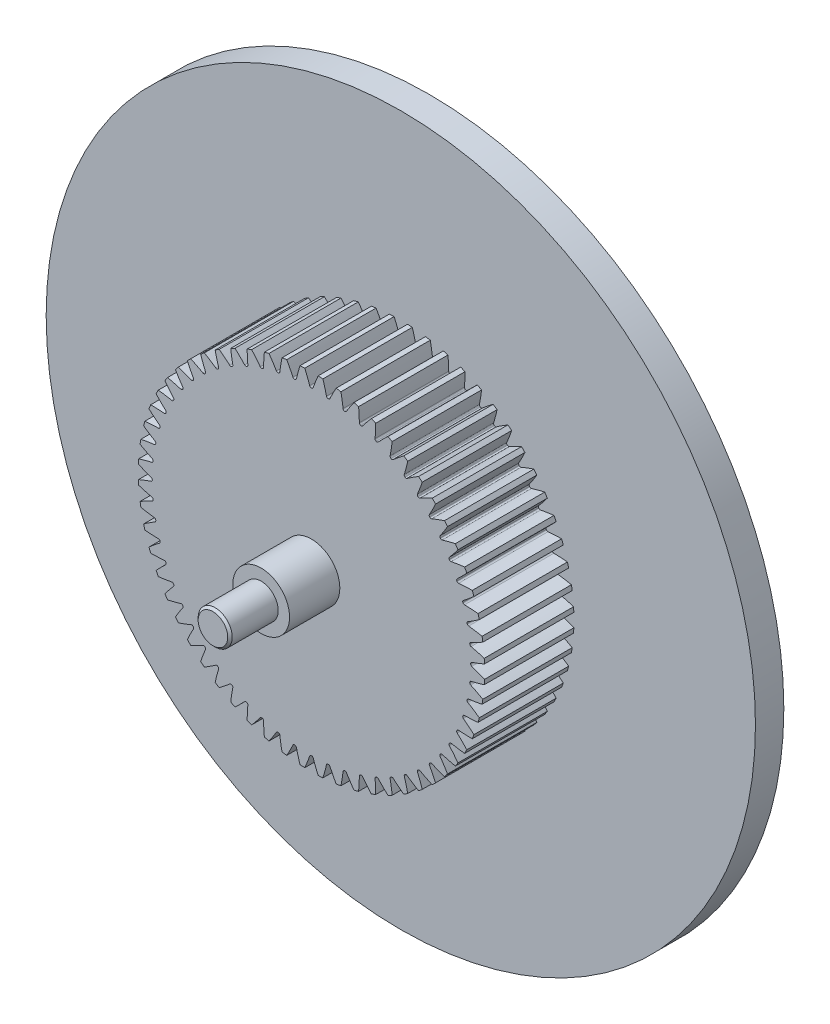
SolidWorks part; units mm, degrees
ref_plane "Front Plane" through (0, 0, 0) normal (0, 0, 1) x (1, 0, 0)
ref_plane "Top Plane" through (0, 0, 0) normal (0, 1, 0) x (1, 0, 0)
ref_plane "Right Plane" through (0, 0, 0) normal (1, 0, 0) x (0, 0, -1)
sketch "Sketch1" plane through (0, 0, 0) normal (0, 0, 1) x (1, 0, 0)
  line L0 (-762, 0) -> (762, 0) construction
  circle A0 centre (0, 0) radius 15.5 construction
  circle A1 centre (0, 0) radius 15 construction
  circle A2 centre (0, 0) radius 14.25 construction
  circle A3 centre (0, 0) radius 7 construction
  circle A4 centre (0, 0) radius 3 construction
  dimension "D2" = 0.5
  dimension "D3" = 1.25
  dimension "D1" = 1.25
sketch "Sketch2" plane through (0, 0, 0) normal (1, 0, 0) x (0, 0, -1)
  line L0 (0, 0) -> (-3, 0) construction
  line L1 (-3, 0) -> (-8, 0) construction
  dimension "Overall Width" = 8
  dimension "Face Width" = 3
sketch "Sketch4" plane through (0, 0, 0) normal (1, 0, 0) x (0, 0, -1)
  line L0 (-8, 3) -> (-8, 7)
  line L1 (-8, 7) -> (-3, 7) construction
  line L2 (-3, 7) -> (-3, 15.5) construction
  line L3 (-3, 15.5) -> (0, 15.5)
  line L4 (0, 15.5) -> (0, 3)
  line L5 (-3, 7) -> (-3, 0) construction
  line L6 (0, 15.5) -> (0, -15.5) construction
  line L7 (-3, 7) -> (0, 7) construction
  line L8 (-3, 15.5) -> (-8, 15.5)
  line L9 (-8, 15.5) -> (-8, 7)
  line L12 (-8, 3) -> (0, 3)
revolve "Revolve1" add sketch "Sketch4" angle 360 about L1
sketch "Sketch7" plane through (0, 0, 3) normal (0, 0, 1) x (1, 0, 0)
  line L0 (0, 0) -> (0, 15.5) construction
  line L1 (0.3927, 14.9949) -> (0.5873, 15.4889) construction
  line L3 (0.8112, 15.4788) -> (0.785, 14.9794) construction
  line L4 (0.785, 14.9794) -> (0.7458, 14.2305) construction
  line L5 (0, 0) -> (0.7458, 14.2305) construction
  line L6 (0.3927, 14.9949) -> (0, 0) construction
  line L7 (0.3927, 14.9949) -> (0.4057, 15.4947) construction
  line L8 (0.3927, 14.9949) -> (0, 0) construction
  circle A0 centre (0, 0) radius 15.5 construction
  arc A1 (-0.014, 14.25) -> (0.014, 14.25) centre (0, 0) cw
  circle A2 centre (0, 0) radius 14.25 construction
  arc A3 (-0.3927, 14.9949) -> (0.3927, 14.9949) centre (0, 0) cw construction
  circle A4 centre (0, 0) radius 15 construction
  arc A5 (1.0249, 15.4661) -> (0.5973, 15.4885) centre (0, 0) ccw construction
  arc A6 (0.3927, 14.9949) -> (1.1769, 14.9538) centre (0, 0) cw construction
  arc A7 (-0.5973, 15.4885) -> (0.5973, 15.4885) centre (0, 0) cw
  arc A8 (0.156, 14.3515) -> (0.5973, 15.4885) centre (14.3489, 9.4973) cw
  arc A9 (-0.156, 14.3515) -> (-0.5973, 15.4885) centre (-14.3489, 9.4973) ccw
  arc A10 (-0.014, 14.25) -> (-0.156, 14.3515) centre (-0.0141, 14.4) cw
  arc A11 (0.014, 14.25) -> (0.156, 14.3515) centre (0.0141, 14.4) ccw
  point P26 (-0.1216, 14.2495)
  point P29 (0.1216, 14.2495)
  dimension "D4" = 0.15
  dimension "D5" = 15
  dimension "D3" = 20
  dimension "D1" = 1.5708
  dimension "D2" = 0.7854
extrude "Cut-Extrude2" cut sketch "Sketch7" against normal up to next (3 mm away) and the other way up to next (5 mm away)
pattern_circular "CirPattern1" count 60 over 360 about axis through (0, 0, 0) along (0, 0, 1) of "Cut-Extrude2"
sketch "Sketch9" plane through (0, 0, 0) normal (0, 0, -1) x (-1, 0, 0)
  circle A0 centre (0, 0) radius 3
  circle A1 centre (0, 0) radius 31.75
  circle A2 centre (0, 0) radius 3 construction
  dimension "D1" = 63.5
extrude "Boss-Extrude1" add sketch "Sketch9" along normal blind 2.54
sketch "Sketch10" plane through (0, 0, -2.54) normal (0, 0, -1) x (-1, 0, 0)
  circle A0 centre (0, 0) radius 3
  circle A1 centre (0, 0) radius 3 construction
extrude "Boss-Extrude2" add sketch "Sketch10" against normal up to surface (10.54 mm away) up to face at (0, 3, 8)
sketch "Sketch11" plane through (0, 0, 8) normal (0, 0, 1) x (1, 0, 0)
  circle A0 centre (0, 0) radius 2.54
  dimension "D1" = 5.08
extrude "Boss-Extrude3" add sketch "Sketch11" along normal blind 4.5
sketch "Sketch12" plane through (0, 0, 12.5) normal (0, 0, 1) x (1, 0, 0)
  circle A0 centre (0, 0) radius 1.524
  dimension "D1" = 3.048
extrude "Boss-Extrude4" add sketch "Sketch12" along normal blind 4.318
sketch "Sketch13" plane through (0, 0, -2.54) normal (0, 0, -1) x (-1, 0, 0)
  circle A0 centre (0, 0) radius 2.54
  dimension "D1" = 5.08
extrude "Boss-Extrude5" add sketch "Sketch13" along normal blind 2.96
sketch "Sketch14" plane through (0, 0, -5.5) normal (0, 0, -1) x (-1, 0, 0)
  circle A0 centre (0, 0) radius 1.524
  dimension "D1" = 3.048
extrude "Boss-Extrude6" add sketch "Sketch14" along normal blind 4.318
chamfer "Chamfer1" distance 0.2 angle 45 2 edges at (1.524, 0, 16.818) (0, 1.524, -9.818)
equation "\"D1@Sketch1\"=2.5*(\"Pitch Dia.@Sketch1\"/\"Number of Teeth@Sketch1\")"
equation "\"D1@CirPattern1\"=\"Number of Teeth@Sketch1\""
equation "\"D1\"= \"OD@Sketch1\" * .01"
equation "\"D1@Sketch7\"=3.14159*(\"Pitch Dia.@Sketch1\"/\"Number of Teeth@Sketch1\")"
equation "\"D2@Sketch7\"=\"D1@Sketch7\"/2"
equation "\"D4@Sketch7\"=\"D1@Sketch7\"*.0955"
equation "\"D5@Sketch7\"=\"Pitch Dia.@Sketch1\"/2"
